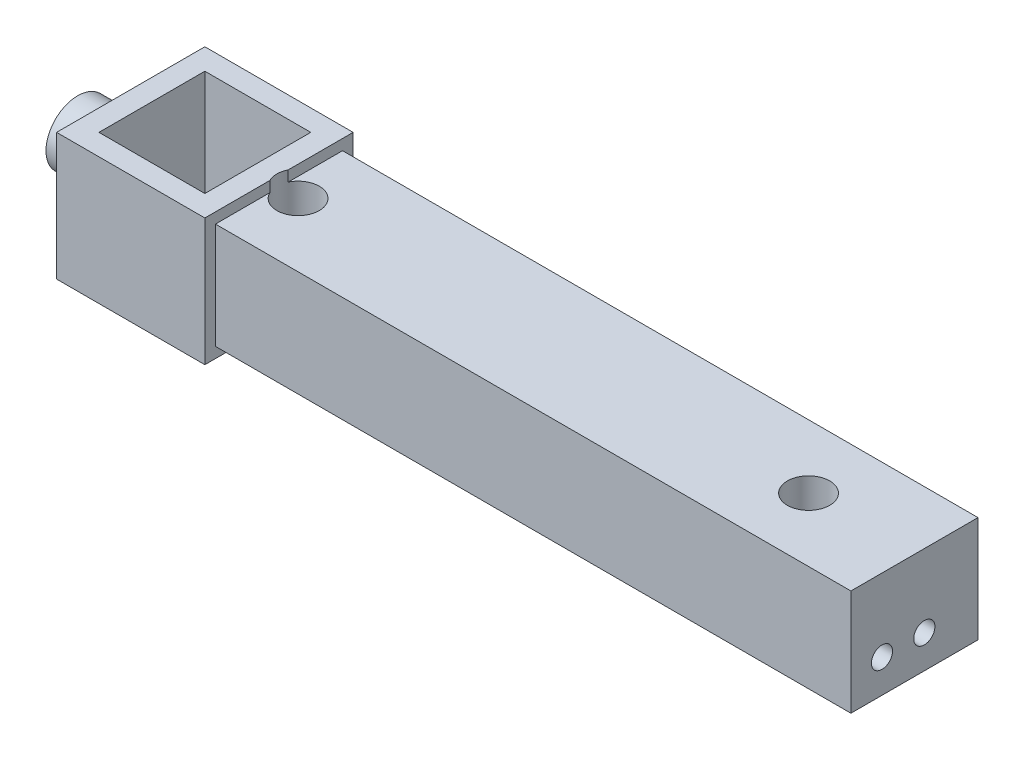
SolidWorks part; units mm, degrees
ref_plane "Front Plane" through (0, 0, 0) normal (0, 0, 1) x (1, 0, 0)
ref_plane "Top Plane" through (0, 0, 0) normal (0, 1, 0) x (1, 0, 0)
ref_plane "Right Plane" through (0, 0, 0) normal (1, 0, 0) x (0, 0, -1)
sketch "Sketch1" plane through (0, 0, 0) normal (0, 1, 0) x (1, 0, 0)
  line L0 (-35, -35) -> (-35, 35)
  line L1 (25, -25) -> (-25, -25)
  line L2 (25, -25) -> (25, 25)
  line L3 (25, 25) -> (-25, 25)
  line L4 (-25, -25) -> (-25, 25)
  line L5 (25, -25) -> (-25, 25) construction
  line L6 (25, 25) -> (-25, -25) construction
  line L7 (35, 35) -> (-35, 35)
  line L8 (35, -35) -> (35, 35)
  line L9 (35, -35) -> (-35, -35)
  point P0 (0, 0)
  dimension "D1" = 50
  dimension "D2" = 50
  dimension "D3" = 10
extrude "Boss-Extrude1" add sketch "Sketch1" along normal blind 60
sketch "Sketch2" plane through (35, 0, 0) normal (1, 0, 0) x (0, 0, -1)
  line L0 (35, 60) -> (35, 0) construction
  line L1 (30, 5) -> (-30, 5)
  line L2 (30, 5) -> (30, 55)
  line L3 (30, 55) -> (-30, 55)
  line L4 (-30, 5) -> (-30, 55)
  line L5 (30, 5) -> (-30, 55) construction
  line L6 (30, 55) -> (-30, 5) construction
  point P0 (0, 30)
  point P8 (35, 30)
  dimension "D1" = 60
  dimension "D2" = 50
extrude "Boss-Extrude2" add sketch "Sketch2" along normal blind 300
sketch "Sketch3" plane through (-35, 0, 0) normal (-1, 0, 0) x (0, 0, 1)
  line L0 (35, 60) -> (35, 0) construction
  circle A0 centre (0, 30) radius 15
  point P4 (35, 30)
  dimension "D1" = 30
extrude "Boss-Extrude3" add sketch "Sketch3" along normal blind 25
sketch "Sketch4" plane through (0, 55, 0) normal (0, 1, 0) x (1, 0, 0)
  line L0 (335, -30) -> (35, -30) construction
  line L1 (335, 30) -> (335, -30) construction
  circle A0 centre (285, 0) radius 10
  dimension "D1" = 30
  dimension "D3" = 20
  dimension "D2" = 50
extrude "Cut-Extrude1" cut sketch "Sketch4" against normal through all
sketch "Sketch5" plane through (0, 55, 0) normal (0, 1, 0) x (1, 0, 0)
  line L0 (25, -25) -> (25, 25) construction
  circle A0 centre (44, 0) radius 10
  dimension "D1" = 20
  dimension "D2" = 19
extrude "Cut-Extrude2" cut sketch "Sketch5" against normal through all both and the other way through all
sketch "Sketch8" plane through (0, 55, 0) normal (0, 1, 0) x (1, 0, 0)
  circle A1 centre (285, 0) radius 10 construction
  circle A2 centre (285, 0) radius 30 construction
  circle A3 centre (255, -0.0373) radius 2.5
  circle A4 centre (299.9677, 25.9994) radius 2.5
  circle A5 centre (300.0323, -25.9621) radius 2.5
  point P14 (285, 0)
  dimension "D1" = 5
  dimension "D2" = 20
  dimension "D3" = 60
  dimension "D4" = 3
extrude "Cut-Extrude3" cut sketch "Sketch8" against normal up to surface (30 mm away) from offset 20 up to face at (285, 5, 10) offset against normal yes
sketch "Sketch9" plane through (335, 0, 0) normal (1, 0, 0) x (0, 0, -1)
  circle A0 centre (-15.3405, 20.6051) radius 5
  circle A1 centre (4.6595, 20.6051) radius 5
  point P4 (0, 0)
  dimension "D1" = 10
  dimension "D2" = 20
extrude "Cut-Extrude4" cut sketch "Sketch9" against normal blind 17
